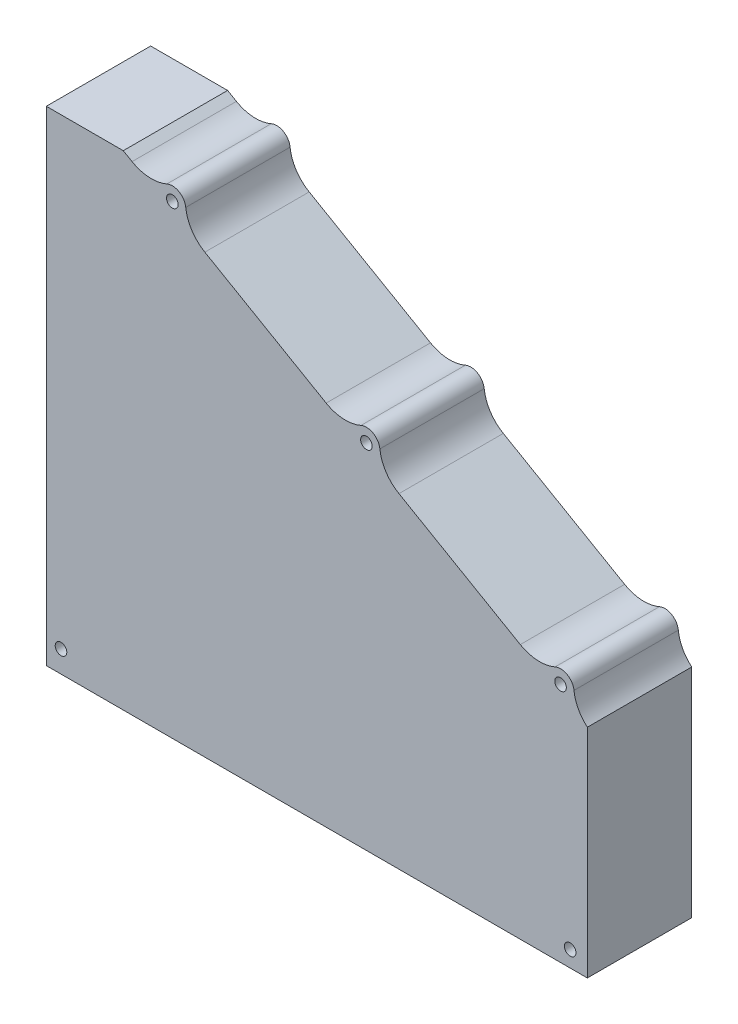
SolidWorks part; units mm, degrees
ref_plane "Front Plane" through (0, 0, 0) normal (0, 0, 1) x (1, 0, 0)
ref_plane "Top Plane" through (0, 0, 0) normal (0, 1, 0) x (1, 0, 0)
ref_plane "Right Plane" through (0, 0, 0) normal (1, 0, 0) x (0, 0, -1)
sketch "Sketch1" plane through (0, 0, 0) normal (0, 0, 1) x (1, 0, 0)
  line L0 (-70, 100) -> (-70, -25.3585)
  line L1 (-70, -25.3585) -> (70, -25.3585)
  line L2 (70, -72.7995) -> (70, 30.8402) construction
  line L3 (70, -25.3585) -> (70, 30.8402)
  line L4 (68, 29.5137) -> (68, -15.1307)
  line L5 (68, -15.1307) -> (51.2417, -23.3585)
  line L6 (53.8122, -22.4229) -> (39.6315, -27.5843) construction
  line L7 (51.2417, -23.3585) -> (-68, -23.3585)
  line L8 (-50.6218, 98) -> (70, 28.359)
  line L9 (70, 28.359) -> (70, 30.8402)
  line L10 (52.647, 40.6871) -> (21.2523, 58.8129)
  line L11 (2.4175, 69.6871) -> (-28.9771, 87.8129)
  line L12 (-47.8119, 98.6871) -> (-50.0859, 100)
  line L13 (-50.0859, 100) -> (-70, 100)
  line L14 (-70, 100) -> (-70, 98)
  line L15 (-70, 98) -> (-50.6218, 98)
  line L16 (-50.6218, 98) -> (70, 28.359)
  line L17 (70, 28.359) -> (70, 30.8402)
  line L18 (52.647, 40.6871) -> (21.2523, 58.8129)
  line L19 (2.4175, 69.6871) -> (-28.9771, 87.8129)
  line L20 (-47.8119, 98.6871) -> (-50.0859, 100)
  line L21 (-50.0859, 100) -> (-70, 100)
  line L22 (-70, 100) -> (-70, 98)
  line L23 (-68, -23.3585) -> (-68, 98)
  line L24 (-50.6218, 98) -> (-70, 98) construction
  line L25 (-50.6218, 98) -> (-68, 98)
  line L66 (-61.6998, -19.7187) -> (-61.6998, -23.3585)
  line L67 (-68, -15.2187) -> (-66.1998, -15.2187)
  circle A0 centre (65.5527, -21.1887) radius 1.5 construction
  circle A1 centre (65.5527, -21.1887) radius 1.5
  circle A2 centre (-37.3945, 94.9821) radius 1.5 construction
  circle A3 centre (-37.3945, 94.9821) radius 1.5
  circle A4 centre (-66.1998, -19.7187) radius 1.5 construction
  circle A5 centre (63.0644, 36.9821) radius 1.5 construction
  circle A6 centre (12.8349, 65.9821) radius 1.5 construction
  circle A7 centre (-66.1998, -19.7187) radius 1.5
  circle A8 centre (63.0644, 36.9821) radius 1.5
  arc A9 (66.5436, 37.3635) -> (70, 30.8402) centre (76.484, 38.4532) ccw
  arc A10 (66.5436, 37.3635) -> (61.6599, 40.1879) centre (63.0644, 36.9821) ccw
  arc A11 (52.647, 40.6871) -> (61.6599, 40.1879) centre (57.647, 49.3474) ccw
  arc A12 (16.3135, 66.3686) -> (21.2523, 58.8129) centre (26.2523, 67.4731) ccw
  arc A13 (16.3135, 66.3686) -> (11.4304, 69.1879) centre (12.8349, 65.9821) ccw
  arc A14 (2.4175, 69.6871) -> (11.4304, 69.1879) centre (7.4175, 78.3474) ccw
  arc A15 (-33.916, 95.3686) -> (-28.9771, 87.8129) centre (-23.9771, 96.4731) ccw
  arc A16 (-33.916, 95.3686) -> (-38.799, 98.1879) centre (-37.3945, 94.9821) ccw
  arc A17 (-47.8119, 98.6871) -> (-38.799, 98.1879) centre (-42.8119, 107.3474) ccw
  arc A18 (66.5436, 37.3635) -> (70, 30.8402) centre (76.484, 38.4532) ccw
  arc A19 (66.5436, 37.3635) -> (61.6599, 40.1879) centre (63.0644, 36.9821) ccw
  arc A20 (52.647, 40.6871) -> (61.6599, 40.1879) centre (57.647, 49.3474) ccw
  arc A21 (16.3135, 66.3686) -> (21.2523, 58.8129) centre (26.2523, 67.4731) ccw
  arc A22 (16.3135, 66.3686) -> (11.4304, 69.1879) centre (12.8349, 65.9821) ccw
  arc A23 (2.4175, 69.6871) -> (11.4304, 69.1879) centre (7.4175, 78.3474) ccw
  arc A24 (-33.916, 95.3686) -> (-28.9771, 87.8129) centre (-23.9771, 96.4731) ccw
  arc A25 (-33.916, 95.3686) -> (-38.799, 98.1879) centre (-37.3945, 94.9821) ccw
  arc A26 (-47.8119, 98.6871) -> (-38.799, 98.1879) centre (-42.8119, 107.3474) ccw
  circle A27 centre (12.8349, 65.9821) radius 1.5
  arc A37 (-68, -15.5944) -> (-63.5538, -23.3585) centre (-66.1998, -19.7187) cw
  dimension "D4" = 3
  dimension "D2" = 2
  dimension "D3" = 2
  dimension "D1" = 0
extrude "Boss-Extrude1" add sketch "Sketch1" along normal blind 25
sketch "Sketch2" plane through (0, 0, 25) normal (0, 0, 1) x (1, 0, 0)
  line L7 (70, -25.3585) -> (70, 30.8402)
  line L8 (52.647, 40.6871) -> (21.2523, 58.8129)
  line L9 (2.4175, 69.6871) -> (-28.9771, 87.8129)
  line L10 (-47.8119, 98.6871) -> (-50.0859, 100)
  line L11 (-50.0859, 100) -> (-70, 100)
  line L12 (-70, 100) -> (-70, -25.3585)
  line L13 (-70, -25.3585) -> (70, -25.3585)
  line L14 (70, -25.3585) -> (70, 30.8402)
  line L15 (52.647, 40.6871) -> (21.2523, 58.8129)
  line L16 (2.4175, 69.6871) -> (-28.9771, 87.8129)
  line L17 (-47.8119, 98.6871) -> (-50.0859, 100)
  line L18 (-50.0859, 100) -> (-70, 100)
  line L19 (-70, 100) -> (-70, -25.3585)
  line L20 (-70, -25.3585) -> (70, -25.3585)
  circle A0 centre (-37.3945, 94.9821) radius 1.5 construction
  circle A1 centre (-37.3945, 94.9821) radius 1.5
  circle A2 centre (12.8349, 65.9821) radius 1.5 construction
  circle A3 centre (12.8349, 65.9821) radius 1.5
  circle A4 centre (63.0644, 36.9821) radius 1.5 construction
  circle A5 centre (63.0644, 36.9821) radius 1.5
  circle A6 centre (65.5527, -21.1887) radius 1.5 construction
  circle A7 centre (65.5527, -21.1887) radius 1.5
  circle A8 centre (-66.1998, -19.7187) radius 1.5 construction
  arc A9 (66.5436, 37.3635) -> (70, 30.8402) centre (76.484, 38.4532) ccw
  arc A10 (66.5436, 37.3635) -> (61.6599, 40.1879) centre (63.0644, 36.9821) ccw
  arc A11 (52.647, 40.6871) -> (61.6599, 40.1879) centre (57.647, 49.3474) ccw
  arc A12 (16.3135, 66.3686) -> (21.2523, 58.8129) centre (26.2523, 67.4731) ccw
  arc A13 (16.3135, 66.3686) -> (11.4304, 69.1879) centre (12.8349, 65.9821) ccw
  arc A14 (2.4175, 69.6871) -> (11.4304, 69.1879) centre (7.4175, 78.3474) ccw
  arc A15 (-33.916, 95.3686) -> (-28.9771, 87.8129) centre (-23.9771, 96.4731) ccw
  arc A16 (-33.916, 95.3686) -> (-38.799, 98.1879) centre (-37.3945, 94.9821) ccw
  arc A17 (-47.8119, 98.6871) -> (-38.799, 98.1879) centre (-42.8119, 107.3474) ccw
  arc A18 (66.5436, 37.3635) -> (70, 30.8402) centre (76.484, 38.4532) ccw
  arc A19 (66.5436, 37.3635) -> (61.6599, 40.1879) centre (63.0644, 36.9821) ccw
  arc A20 (52.647, 40.6871) -> (61.6599, 40.1879) centre (57.647, 49.3474) ccw
  arc A21 (16.3135, 66.3686) -> (21.2523, 58.8129) centre (26.2523, 67.4731) ccw
  arc A22 (16.3135, 66.3686) -> (11.4304, 69.1879) centre (12.8349, 65.9821) ccw
  arc A23 (2.4175, 69.6871) -> (11.4304, 69.1879) centre (7.4175, 78.3474) ccw
  arc A24 (-33.916, 95.3686) -> (-28.9771, 87.8129) centre (-23.9771, 96.4731) ccw
  arc A25 (-33.916, 95.3686) -> (-38.799, 98.1879) centre (-37.3945, 94.9821) ccw
  arc A26 (-47.8119, 98.6871) -> (-38.799, 98.1879) centre (-42.8119, 107.3474) ccw
  circle A27 centre (-66.1998, -19.7187) radius 1.5
  dimension "D1" = 0
extrude "Boss-Extrude2" add sketch "Sketch2" along normal blind 2
sketch "Sketch3" plane through (0, -25.3585, 0) normal (0, -1, 0) x (-1, 0, 0)
  line L0 (70, -27) -> (70, 0) construction
  line L1 (50, -22) -> (47, -22)
  line L2 (50, -22) -> (50, -5)
  line L3 (50, -5) -> (47, -5)
  line L4 (47, -22) -> (47, -5)
  line L5 (70, -27) -> (-70, -27) construction
  line L6 (70, 0) -> (-70, 0) construction
  dimension "D1" = 5
  dimension "D2" = 3
  dimension "D3" = 20
  dimension "D4" = 5
extrude "Cut-Extrude1" cut sketch "Sketch3" against normal up to next (2 mm away)
pattern_linear "LPattern1" count 7 spacing 15 along (1, 0, 0) of "Cut-Extrude1"
